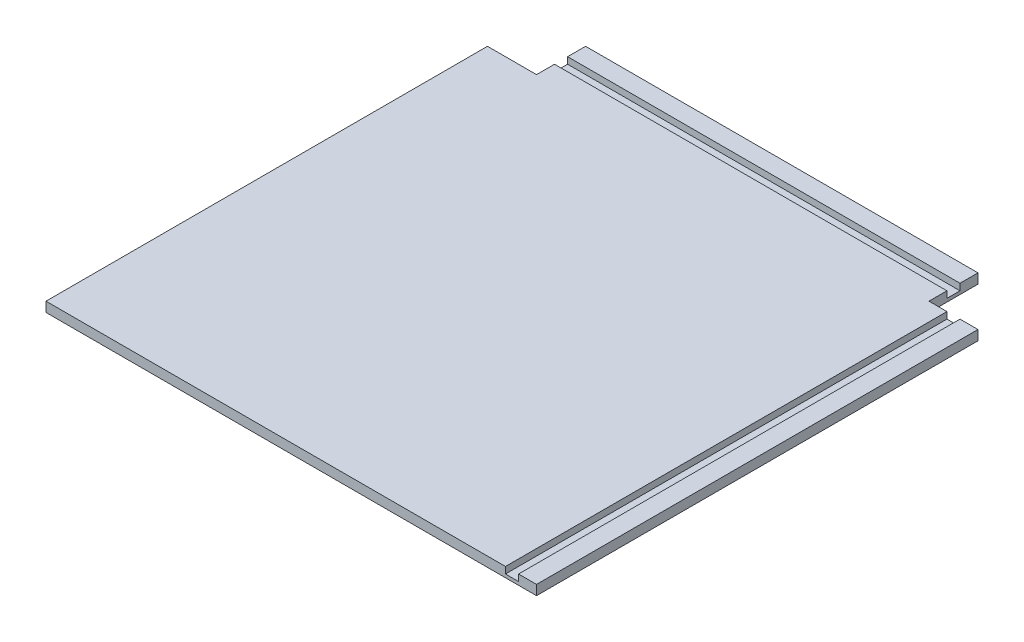
SolidWorks part; units mm, degrees
material "Oak"
ref_plane "Front Plane" through (0, 0, 0) normal (0, 0, 1) x (1, 0, 0)
ref_plane "Top Plane" through (0, 0, 0) normal (0, 1, 0) x (1, 0, 0)
ref_plane "Right Plane" through (0, 0, 0) normal (1, 0, 0) x (0, 0, -1)
sketch "Sketch2" plane through (0, 0, 0) normal (0, 1, 0) x (1, 0, 0)
  line L0 (0, -55) -> (0, 55) construction
  line L1 (-375, -375) -> (375, -375)
  line L2 (-375, -375) -> (-375, 375)
  line L3 (-375, 375) -> (375, 375)
  line L4 (375, -375) -> (375, 375)
  line L5 (-375, -375) -> (375, 375) construction
  line L6 (-375, 375) -> (375, -375) construction
  line L7 (-375, 375) -> (-300, 375)
  line L8 (-375, 375) -> (-375, 300)
  line L9 (-375, 300) -> (-300, 300)
  line L10 (-300, 375) -> (-300, 300)
  line L11 (375, 300) -> (300, 300)
  line L12 (300, 375) -> (300, 300)
  line L13 (375, 375) -> (300, 375)
  line L14 (375, 375) -> (375, 300)
  point P0 (0, 0)
  dimension "D1" = 750
  dimension "D2" = 75
extrude "Boss-Extrude1" add sketch "Sketch2" along normal blind 15 contours L12 L3 L10 L9 L2 L1 L4 L11
sketch "Sketch3" plane through (0, 0, 375) normal (0, 0, 1) x (1, 0, 0)
  line L0 (-375, 15) -> (-300, 15) construction
  line L1 (-337.5, 15) -> (-337.5, 0) construction
  line L2 (-375, 0) -> (375, 0) construction
  line L3 (-347.5, 15) -> (-347.5, 5)
  line L4 (-347.5, 5) -> (-327.5, 5)
  line L5 (-327.5, 5) -> (-327.5, 15)
  line L6 (-327.5, 15) -> (-347.5, 15)
  line L7 (0, -7.7) -> (0, 7.7) construction
  line L8 (327.5, 5) -> (327.5, 15)
  line L9 (347.5, 5) -> (327.5, 5)
  line L10 (347.5, 15) -> (347.5, 5)
  line L11 (327.5, 15) -> (347.5, 15)
  line M8 (375, 15) -> (-375, 15)
  dimension "D1" = 10
  dimension "D2" = 20
extrude "Cut-Extrude1" cut sketch "Sketch3" against normal up to vertex (675 mm away) contours L10 L8 L9 M8
sketch "Sketch4" plane through (375, 0, 0) normal (1, 0, 0) x (0, 0, -1)
  line L0 (337.5, 0) -> (337.5, 15) construction
  line L1 (375, 0) -> (300, 0) construction
  line L2 (375, 15) -> (300, 15) construction
  line L8 (327.5, 15) -> (347.5, 15)
  line L9 (327.5, 15) -> (327.5, 5)
  line L10 (327.5, 5) -> (347.5, 5)
  line L11 (347.5, 15) -> (347.5, 5)
  dimension "D1" = 20
  dimension "D2" = 10
extrude "Cut-Extrude2" cut sketch "Sketch4" against normal through all
equation "\"A\"= 75cm"
equation "\"B\"= 15mm"
equation "\"D1@Sketch2\"=\"A\""
equation "\"D1@Boss-Extrude1\"=\"B\""
